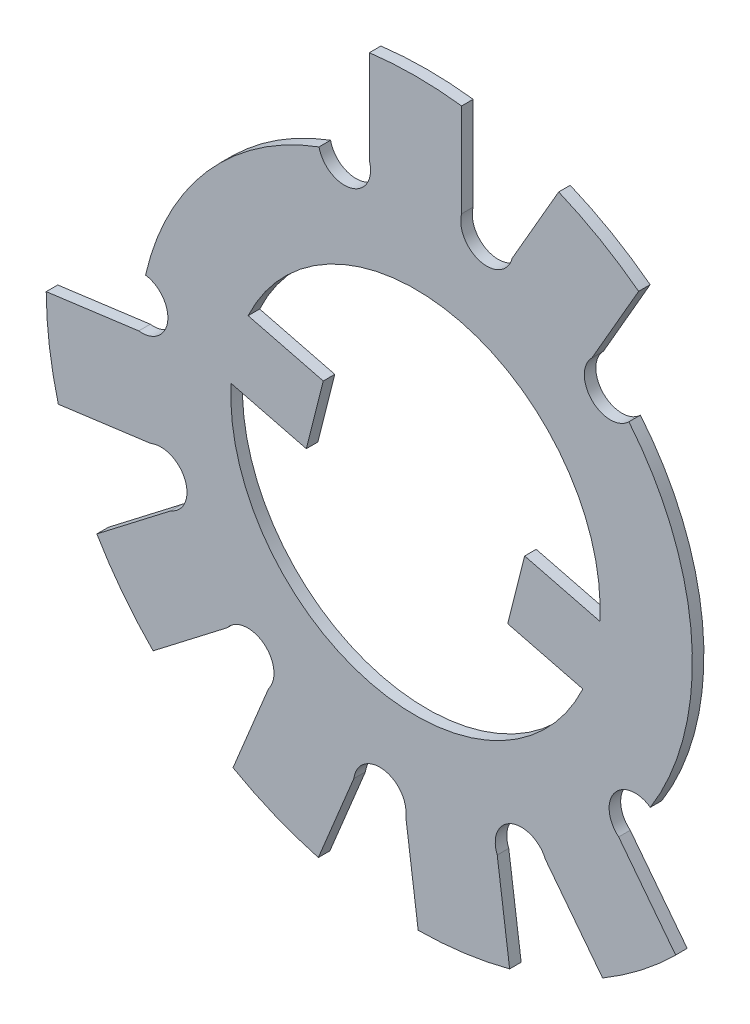
SolidWorks part; units mm, degrees
ref_plane "Face" through (0, 0, 0) normal (0, 0, 1) x (1, 0, 0)
ref_plane "Dessus" through (0, 0, 0) normal (0, 1, 0) x (1, 0, 0)
ref_plane "Droite" through (0, 0, 0) normal (1, 0, 0) x (0, 0, -1)
sketch "Esquisse1" plane through (0, 0, 0) normal (0, 0, 1) x (1, 0, 0)
  line L0 (0, 0) -> (0, 19.5761) construction
  line L1 (0, 0) -> (1.3955, 1.3955) construction
  line L2 (1.9991, 15.8746) -> (1.9991, 11.8301)
  line L3 (0, 0) -> (12.3609, 21.4097) construction
  line L4 (-1.9991, 11.8323) -> (-1.9991, 15.8746)
  line L5 (4.1862, 11.2489) -> (6.2054, 14.7508)
  line L6 (9.6691, 12.7535) -> (7.6488, 9.2498)
  line L7 (-11.4682, -3.5253) -> (-15.4754, -4.057)
  line L8 (-16.0013, -0.0935) -> (-11.992, 0.4385)
  line L9 (-13.8069, -8.0883) -> (-10.6019, -5.6214)
  line L10 (-8.1649, -8.7911) -> (-11.3682, -11.2567)
  line L11 (-7.9063, -13.9119) -> (-6.366, -10.1722)
  line L12 (-2.6699, -11.697) -> (-4.2094, -15.4347)
  line L13 (0.1166, -16.0012) -> (-0.4212, -11.9926)
  line L14 (3.5418, -11.4632) -> (4.0793, -15.4696)
  line L15 (8.1082, -13.7953) -> (5.6366, -10.5938)
  line L16 (8.8028, -8.1523) -> (11.273, -11.352)
  line L17 (7.9862, -0.4691) -> (4.7303, 0.3529)
  line L18 (0.0075, 0) -> (9.7672, -12.6729) construction
  line L19 (-0.0128, -0.0017) -> (-15.8627, -2.0918) construction
  line L21 (3.9959, -2.5559) -> (7.2519, -3.3778)
  line L22 (-7.2519, 3.3778) -> (-3.9959, 2.5559)
  line L23 (-3.9959, 2.5559) -> (-4.7303, -0.3529)
  line L24 (-4.7303, -0.3529) -> (-7.9862, 0.4691)
  line L25 (4.7303, 0.3529) -> (3.9959, -2.5559)
  arc A0 (-4.1799, 11.2485) -> (-11.6971, 2.679) centre (0, 0) ccw
  arc A1 (7.9862, -0.4691) -> (-7.2519, 3.3778) centre (0, 0) ccw
  arc A2 (1.9991, 15.8746) -> (-1.9991, 15.8746) centre (0, 0) ccw
  arc A3 (9.6691, 12.7535) -> (6.2054, 14.7508) centre (0.0075, 0) ccw
  arc A4 (-16.0013, -0.0935) -> (-15.4754, -4.057) centre (-0.0017, 0.0128) ccw
  arc A5 (-13.8069, -8.0883) -> (-11.3682, -11.2567) centre (-0.0079, 0.0102) ccw
  arc A6 (-7.9063, -13.9119) -> (-4.2094, -15.4347) centre (-0.012, 0.0049) ccw
  arc A7 (0.1166, -16.0012) -> (4.0793, -15.4696) centre (-0.0128, -0.0017) ccw
  arc A8 (8.1082, -13.7953) -> (11.273, -11.352) centre (-0.0102, -0.0079) ccw
  arc A9 (-11.992, 0.4385) -> (-11.6971, 2.679) centre (-11.8583, 1.5605) ccw
  arc A10 (8.8028, -8.1523) -> (10.1747, -6.358) centre (9.52, -7.2791) cw
  arc A11 (-1.9991, 11.8323) -> (-4.1799, 11.2485) centre (-3.0759, 11.4895) cw
  arc A14 (10.1747, -6.358) -> (9.2456, 7.6464) centre (0, 0) ccw
  arc A15 (-7.9862, 0.4691) -> (7.2519, -3.3778) centre (0, 0) ccw
  arc A16 (1.9991, 11.8301) -> (4.1862, 11.2489) centre (3.0927, 11.5395) ccw
  arc A17 (-11.4682, -3.5253) -> (-10.6019, -5.6214) centre (-11.0351, -4.5733) cw
  arc A18 (-8.1649, -8.7911) -> (-6.366, -10.1722) centre (-7.2654, -9.4816) cw
  arc A19 (-2.6699, -11.697) -> (-0.4212, -11.9926) centre (-1.5455, -11.8448) cw
  arc A20 (3.5418, -11.4632) -> (5.6366, -10.5938) centre (4.5892, -11.0285) cw
  arc A21 (9.2456, 7.6464) -> (7.6488, 9.2498) centre (8.4472, 8.4481) cw
  dimension "D1" = 24
  dimension "D2" = 1.13
  dimension "D4" = 32
  dimension "D5" = 1.13
  dimension "D6" = 1.13
  dimension "D7" = 11.9978
  dimension "D8" = 1.1315
  dimension "D9" = 1.134
  dimension "D10" = 1.134
  dimension "D11" = 1.134
  dimension "D12" = 1.134
  dimension "D13" = 0.0075
  dimension "D3" = 30
  dimension "D14" = 9.52
  dimension "D15" = 3.0759
  dimension "D16" = 11.6971
extrude "Extrusion1" add sketch "Esquisse1" along normal blind 0.5
